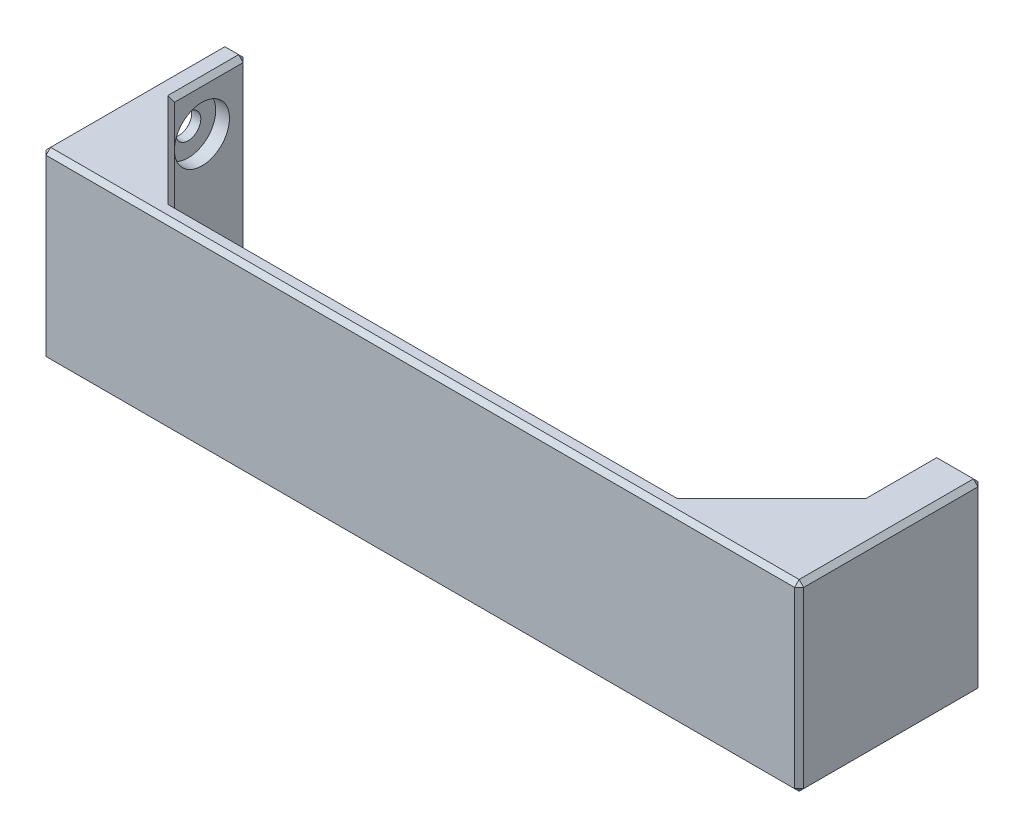
SolidWorks part; units mm, degrees
ref_plane "Front Plane" through (0, 0, 0) normal (0, 0, 1) x (1, 0, 0)
ref_plane "Top Plane" through (0, 0, 0) normal (0, 1, 0) x (1, 0, 0)
ref_plane "Right Plane" through (0, 0, 0) normal (1, 0, 0) x (0, 0, -1)
ref_plane "Plane1" through (0, 20, 0) normal (0, 1, 0) x (1, 0, 0)
sketch "Sketch1" plane through (0, 20, 0) normal (0, 1, 0) x (1, 0, 0)
  line L0 (5, 4) -> (5, -20)
  line L1 (5, -20) -> (155.2, -20)
  line L2 (155.2, -20) -> (155.2, 4)
  line L3 (155.2, 4) -> (135.2, -16)
  line L4 (135.2, -16) -> (25, -16)
  line L5 (25, -16) -> (5, 4)
extrude "Boss-Extrude1" add sketch "Sketch1" against normal blind 40
sketch "Sketch2" plane through (5, 0, 0) normal (-1, 0, 0) x (0, 0, 1)
  line L0 (20, 20) -> (20, -20)
  line L1 (20, -20) -> (-20, -20)
  line L2 (-20, -20) -> (-20, 20)
  line L3 (-20, 20) -> (20, 20)
extrude "Boss-Extrude2" add sketch "Sketch2" along normal blind 5
sketch "Sketch3" plane through (155.2, 0, 0) normal (1, 0, 0) x (0, 0, -1)
  line L0 (20, 20) -> (20, -20)
  line L1 (20, -20) -> (-20, -20)
  line L2 (-20, -20) -> (-20, 20)
  line L3 (-20, 20) -> (20, 20)
extrude "Boss-Extrude3" add sketch "Sketch3" along normal blind 10
ref_plane "Plane2" through (0, -15, 0) normal (0, -1, 0) x (1, 0, 0)
sketch "Sketch4" plane through (0, -15, 0) normal (0, -1, 0) x (1, 0, 0)
  line L0 (155.2, -4) -> (155.2, 16)
  line L1 (155.2, 16) -> (135.2, 16)
  line L2 (135.2, 16) -> (155.2, -4)
extrude "Cut-Extrude1" cut sketch "Sketch4" against normal blind 30
ref_plane "Plane3" through (0, 15, 0) normal (0, 1, 0) x (1, 0, 0)
sketch "Sketch5" plane through (0, 15, 0) normal (0, 1, 0) x (1, 0, 0)
  line L0 (5, 4) -> (5, -16)
  line L1 (5, -16) -> (25, -16)
  line L2 (25, -16) -> (5, 4)
extrude "Cut-Extrude2" cut sketch "Sketch5" against normal blind 30
hole_wizard "CBORE for M10 Hex Head Bolt1" positions "Sketch7" profile "Sketch6" counterbore size "M10" standard "ANSI Metric"
sketch "Sketch7" plane through (0, 0, 0) normal (-1, 0, 0) x (0, 0, 1)
  point P0 (10, -10)
sketch "Sketch6" plane through (0, -10, 10) normal (0, 1, 0) x (0, 0, 1)
  line L0 (0, 0) -> (0, 5)
  line L1 (0, 5) -> (6, 5)
  line L2 (6, 5) -> (6, 2)
  line L3 (6, 2) -> (2.75, 2)
  line L4 (2.75, 2) -> (2.75, 0)
  line L5 (2.75, 0) -> (0, 0)
  line L10 (0, 5) -> (-6, 5) construction
  line L11 (0, -6.35) -> (0, 107.95) construction
  dimension "Hole Dia." = 12
  dimension "Hole Depth" = 5
  dimension "C'Bore Dia." = 5.5
  dimension "C'Bore Depth" = 2
  dimension "Drill Angle" = 180
hole_wizard "CBORE for M5 Hex Head Bolt1" positions "Sketch9" profile "Sketch8" counterbore size "M5" standard "ANSI Metric"
sketch "Sketch9" plane through (5, 0, 0) normal (1, 0, 0) x (0, 0, -1)
  point P0 (10, 10)
sketch "Sketch8" plane through (5, 10, -10) normal (0, 1, 0) x (0, 0, -1)
  line L0 (0, 0) -> (0, 5)
  line L1 (0, 5) -> (2.75, 5)
  line L3 (2.75, 5) -> (2.75, 3)
  line L4 (2.75, 3) -> (6, 3)
  line L5 (6, 3) -> (6, 0)
  line L7 (6, 0) -> (0, 0)
  line L11 (0, -6.35) -> (0, 107.95) construction
  dimension "Thru Hole Dia." = 5.5
  dimension "Thru Hole Depth" = 5
  dimension "C'Bore Dia." = 12
  dimension "C'Bore Depth" = 3
chamfer "Chamfer1" distance 1 angle 45 29 edges at (155.2, -20, -12) (145.2, -15, 6) (145.2, -20, 6) (145.2, 15, 6) (145.2, 20, 6) (80.1, 20, 16) (80.1, -20, 16) (15, 15, 6) (15, 20, 6) (15, -15, 6) (15, -20, 6) (5, -20, -12) (2.5, -20, -20) (0, -20, 0) (5, 0, -20) (160.2, -20, -20) (82.6, 20, 20) (82.6, -20, 20) (165.2, -20, 0) (155.2, 20, -12) (5, 20, -12) (155.2, 0, -20) (0, 0, 20) (2.5, 20, -20) (0, 20, 0) (165.2, 0, -20) (165.2, 0, 20) (160.2, 20, -20) (165.2, 20, 0)
